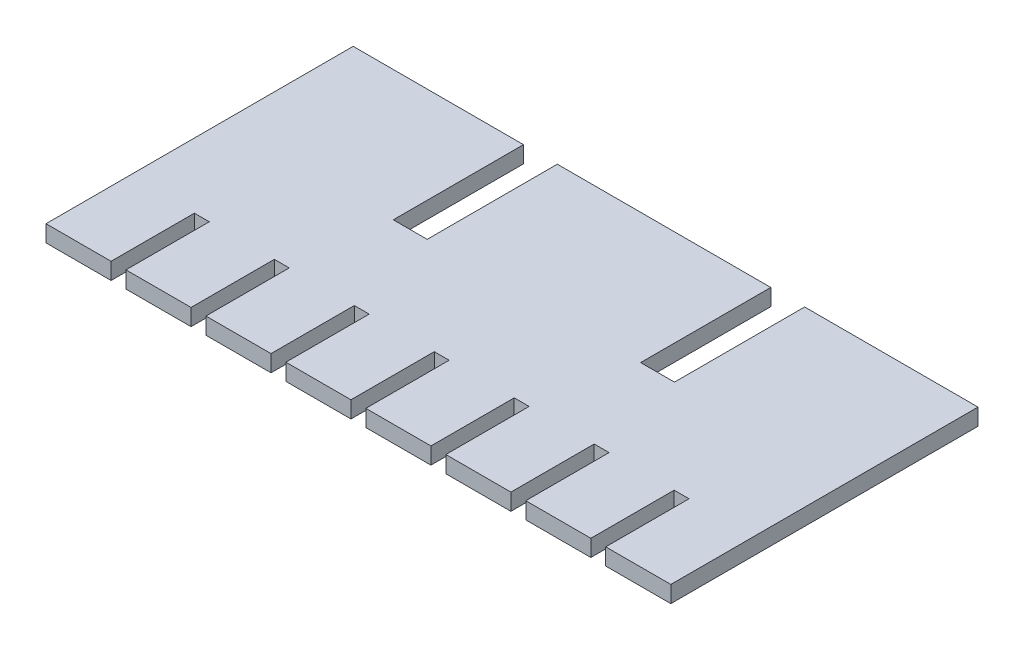
SolidWorks part; units mm, degrees
ref_plane "Front Plane" through (0, 0, 0) normal (0, 0, 1) x (1, 0, 0)
ref_plane "Top Plane" through (0, 0, 0) normal (0, 1, 0) x (1, 0, 0)
ref_plane "Right Plane" through (0, 0, 0) normal (1, 0, 0) x (0, 0, -1)
sketch "Sketch1" plane through (0, 0, 0) normal (0, 1, 0) x (1, 0, 0)
  line L0 (0, 0) -> (0, -29.5)
  line L1 (0, -29.5) -> (6.25, -29.5)
  line L2 (6.25, -29.5) -> (6.25, -21.5)
  line L3 (6.25, -21.5) -> (7.679, -21.5)
  line L4 (7.679, -21.5) -> (7.679, -29.5)
  line L5 (7.679, -29.5) -> (13.929, -29.5)
  line L6 (13.929, -29.5) -> (13.929, -21.5)
  line L7 (13.929, -21.5) -> (15.358, -21.5)
  line L8 (15.358, -21.5) -> (15.358, -29.5)
  line L9 (15.358, -29.5) -> (21.608, -29.5)
  line L10 (21.608, -29.5) -> (21.608, -21.5)
  line L11 (21.608, -21.5) -> (23.037, -21.5)
  line L12 (23.037, -21.5) -> (23.037, -29.5)
  line L13 (23.037, -29.5) -> (29.287, -29.5)
  line L14 (29.287, -29.5) -> (29.287, -21.5)
  line L15 (29.287, -21.5) -> (30.716, -21.5)
  line L16 (30.716, -21.5) -> (30.716, -29.5)
  line L17 (30.716, -29.5) -> (36.966, -29.5)
  line L18 (36.966, -29.5) -> (36.966, -21.5)
  line L19 (36.966, -21.5) -> (38.395, -21.5)
  line L20 (38.395, -21.5) -> (38.395, -29.5)
  line L21 (38.395, -29.5) -> (44.645, -29.5)
  line L22 (44.645, -29.5) -> (44.645, -21.5)
  line L23 (44.645, -21.5) -> (46.074, -21.5)
  line L24 (46.074, -21.5) -> (46.074, -29.5)
  line L25 (46.074, -29.5) -> (52.324, -29.5)
  line L26 (52.324, -29.5) -> (52.324, -21.5)
  line L27 (52.324, -21.5) -> (53.753, -21.5)
  line L28 (53.753, -21.5) -> (53.753, -29.5)
  line L29 (53.753, -29.5) -> (60.003, -29.5)
  line L30 (60.003, -29.5) -> (60.003, 0)
  line L31 (60.003, 0) -> (43.353, 0)
  line L32 (43.353, 0) -> (43.353, -12.5)
  line L33 (43.353, -12.5) -> (40.103, -12.5)
  line L34 (40.103, -12.5) -> (40.103, 0)
  line L35 (40.103, 0) -> (19.603, 0)
  line L36 (19.603, 0) -> (19.603, -12.5)
  line L37 (19.603, -12.5) -> (16.353, -12.5)
  line L38 (16.353, -12.5) -> (16.353, 0)
  line L39 (16.353, 0) -> (0, 0)
extrude "Boss-Extrude1" add sketch "Sketch1" along normal blind 1.6
